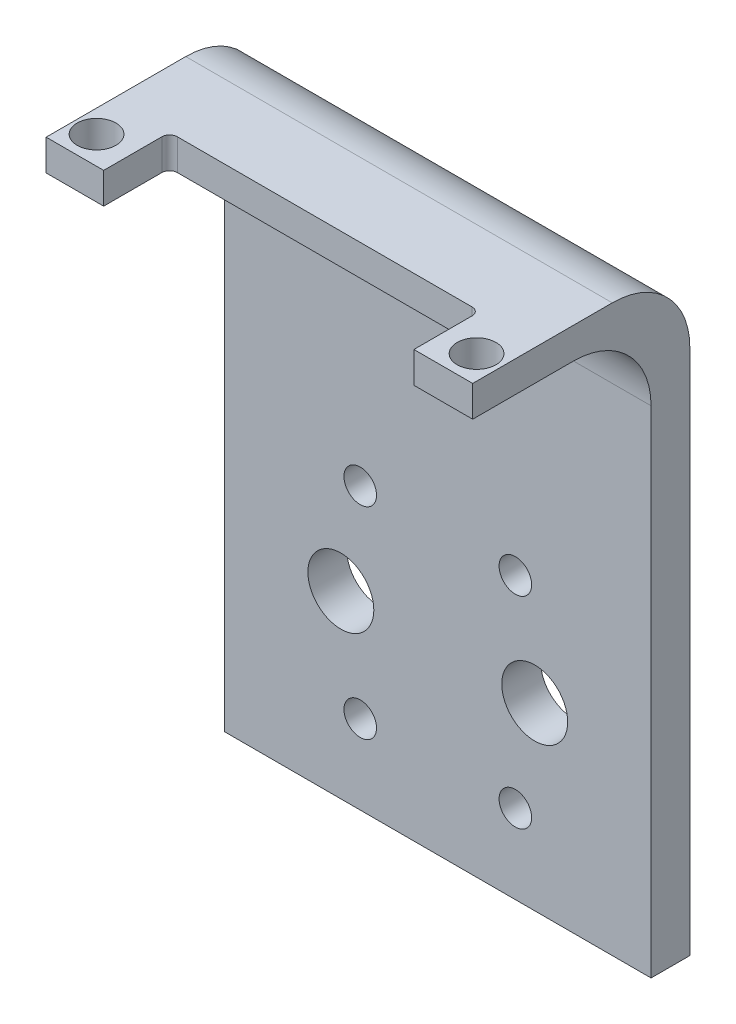
SolidWorks part; units mm, degrees
ref_plane "Front Plane" through (0, 0, 0) normal (0, 0, 1) x (1, 0, 0)
ref_plane "Top Plane" through (0, 0, 0) normal (0, 1, 0) x (1, 0, 0)
ref_plane "Right Plane" through (0, 0, 0) normal (1, 0, 0) x (0, 0, -1)
sketch "Sketch1" plane through (0, 0, 0) normal (0, 0, 1) x (1, 0, 0)
  line L0 (-50.4176, -29.8314) -> (-27.4176, -29.8314)
  line L5 (27.5824, -29.8314) -> (50.5824, -29.8314)
  line L6 (50.5824, -29.8314) -> (50.5824, 25.1686)
  line L7 (45.5824, 30.1686) -> (-45.4176, 30.1686)
  line L8 (-50.4176, 25.1686) -> (-50.4176, -29.8314)
  arc A0 (27.5824, -29.8314) -> (-27.4176, -29.8314) centre (0.0824, -88.7275) ccw
  arc A1 (50.5824, 25.1686) -> (45.5824, 30.1686) centre (45.5824, 25.1686) ccw
  arc A2 (-45.4176, 30.1686) -> (-50.4176, 25.1686) centre (-45.4176, 25.1686) ccw
  circle A3 centre (12.5824, -0.5199) radius 4.25
  circle A4 centre (10.0824, -13.5199) radius 2.1
  circle A5 centre (-9.9176, -13.5199) radius 2.1
  circle A6 centre (-12.4176, -0.5199) radius 4.25
  circle A7 centre (-9.9176, 12.4801) radius 2.1
  circle A8 centre (10.0824, 12.4801) radius 2.1
extrude "Boss-Extrude1" add sketch "Sketch1" along normal blind 5
sketch "Sketch2" plane through (0, 0, 5) normal (0, 0, 1) x (1, 0, 0)
  line L0 (0.0824, 16.4801) -> (0.0824, 33.7046) construction
  line L1 (-50.4176, 30.1686) -> (-27.4176, 30.1686)
  line L2 (-50.4176, 30.1686) -> (-50.4176, -29.8314)
  line L3 (-50.4176, -29.8314) -> (-27.4176, -29.8314)
  line L4 (-27.4176, 30.1686) -> (-27.4176, -29.8314)
  line L5 (-50.4176, 30.1686) -> (-27.4176, -29.8314) construction
  line L6 (-50.4176, -29.8314) -> (-27.4176, 30.1686) construction
  line L7 (18.5824, 16.4801) -> (-18.4176, 16.4801) construction
  line L8 (50.5824, -29.8314) -> (27.5824, 30.1686) construction
  line L9 (50.5824, 30.1686) -> (27.5824, -29.8314) construction
  line L10 (27.5824, 30.1686) -> (27.5824, -29.8314)
  line L11 (50.5824, -29.8314) -> (27.5824, -29.8314)
  line L12 (50.5824, 30.1686) -> (50.5824, -29.8314)
  line L13 (50.5824, 30.1686) -> (27.5824, 30.1686)
  point P4 (-38.9176, 0.1686)
  point P14 (39.0824, 0.1686)
extrude "Cut-Extrude1" cut sketch "Sketch2" against normal blind 10
fillet "Fillet1" radius 5 1 edges at (27.5824, 30.1686, 2.5)
fillet "Fillet2" radius 5 1 edges at (-27.4176, 30.1686, 2.5)
sketch "Esquisse1" plane through (0, 0, 5) normal (0, 0, 1) x (1, 0, 0)
  line L0 (-30.4729, -23.7275) -> (30.6377, -23.7275)
  line L1 (30.6377, -23.7275) -> (30.6377, -34.159)
  line L2 (30.6377, -34.159) -> (-30.4729, -34.159)
  line L3 (-30.4729, -34.159) -> (-30.4729, -23.7275)
  point P3 (0.0824, -23.7275)
extrude "Enlèv. mat.-Extru.1" cut sketch "Esquisse1" against normal blind 10
sketch "Esquisse3" plane through (0, 30.1686, 0) normal (0, 1, 0) x (1, 0, 0)
  line L0 (-22.4176, 0) -> (-22.4176, -27)
  line L1 (-22.4176, -27) -> (22.5824, -27)
  line L2 (22.5824, -27) -> (22.5824, 0)
  line L3 (22.5824, -5) -> (22.5824, 0) construction
  line L4 (-22.4176, 0) -> (-22.4176, -5) construction
  line L6 (-22.4176, 0) -> (22.5824, 0)
  line L7 (22.5824, -5) -> (-22.4176, -5) construction
  point P8 (-22.4176, 0)
  point P9 (22.5824, 0)
  dimension "D1" = 22
extrude "Boss.-Extru.1" [suppressed] add sketch "Esquisse3" along normal blind 4
fillet "Congé1" [suppressed] radius 10
sketch "Esquisse5" plane through (0, 30.1686, 0) normal (0, 1, 0) x (1, 0, 0)
  line L0 (-27.4176, -5) -> (-27.4176, 0) construction
  line L2 (-27.4176, 0) -> (27.5824, 0)
  line L3 (-27.4176, 0) -> (-27.4176, -5)
  line L4 (-27.4176, -5) -> (27.5824, -5)
  line L12 (27.5824, 0) -> (27.5824, -5)
  line L13 (27.5824, 0) -> (27.5824, -5) construction
extrude "Boss.-Extru.3" add sketch "Esquisse5" along normal blind 20 and the other way blind 9
sketch "Esquisse6" plane through (0, 50.1686, 0) normal (0, 1, 0) x (1, 0, 0)
  line L1 (27.5824, -5) -> (27.5824, 0) construction
  line L2 (-27.4176, 0) -> (27.5824, 0)
  line L3 (-27.4176, 0) -> (-27.4176, -28)
  line L12 (-27.4176, -28) -> (27.5824, -28)
  line L13 (27.5824, 0) -> (27.5824, -28)
  line L14 (-27.4176, 0) -> (-27.4176, -5) construction
  line L15 (27.5824, 0) -> (-27.4176, 0) construction
  dimension "D1" = 28
extrude "Boss.-Extru.4" add sketch "Esquisse6" along normal blind 4
fillet "Congé2" radius 10 2 edges at (0.0824, 54.1686, 0) (0.0824, 50.1686, 5)
sketch "Esquisse11" plane through (0, 54.1686, 0) normal (0, 1, 0) x (1, 0, 0)
  line L0 (0, 32.9713) -> (0, -32.9713) construction
  line L1 (-31.4519, -30) -> (37.6459, -30) construction
  line L2 (-27.4176, -28) -> (27.5824, -28) construction
  line L3 (-32.7993, -24.42) -> (30.8388, -24.42) construction
  line L4 (-19, -19.5) -> (19, -19.5)
  line L5 (-20, -20.5) -> (-20, -40.5)
  line L6 (-20, -40.5) -> (20, -40.5)
  line L7 (20, -20.5) -> (20, -40.5)
  arc A0 (19, -19.5) -> (20, -20.5) centre (19, -20.5) cw
  arc A1 (-19, -19.5) -> (-20, -20.5) centre (-19, -20.5) ccw
  circle A2 centre (-24.5, -24.42) radius 2.5
  circle A3 centre (24.5, -24.42) radius 2.5
  dimension "D6" = 1
  dimension "D9" = 5
  dimension "D1" = 2
  dimension "D2" = 20
  dimension "D3" = 40
  dimension "D4" = 10.5
  dimension "D5" = 10.5
  dimension "D7" = 4.92
  dimension "D8" = 4.5
extrude "Enlèv. mat.-Extru.2" cut sketch "Esquisse11" against normal blind 4
